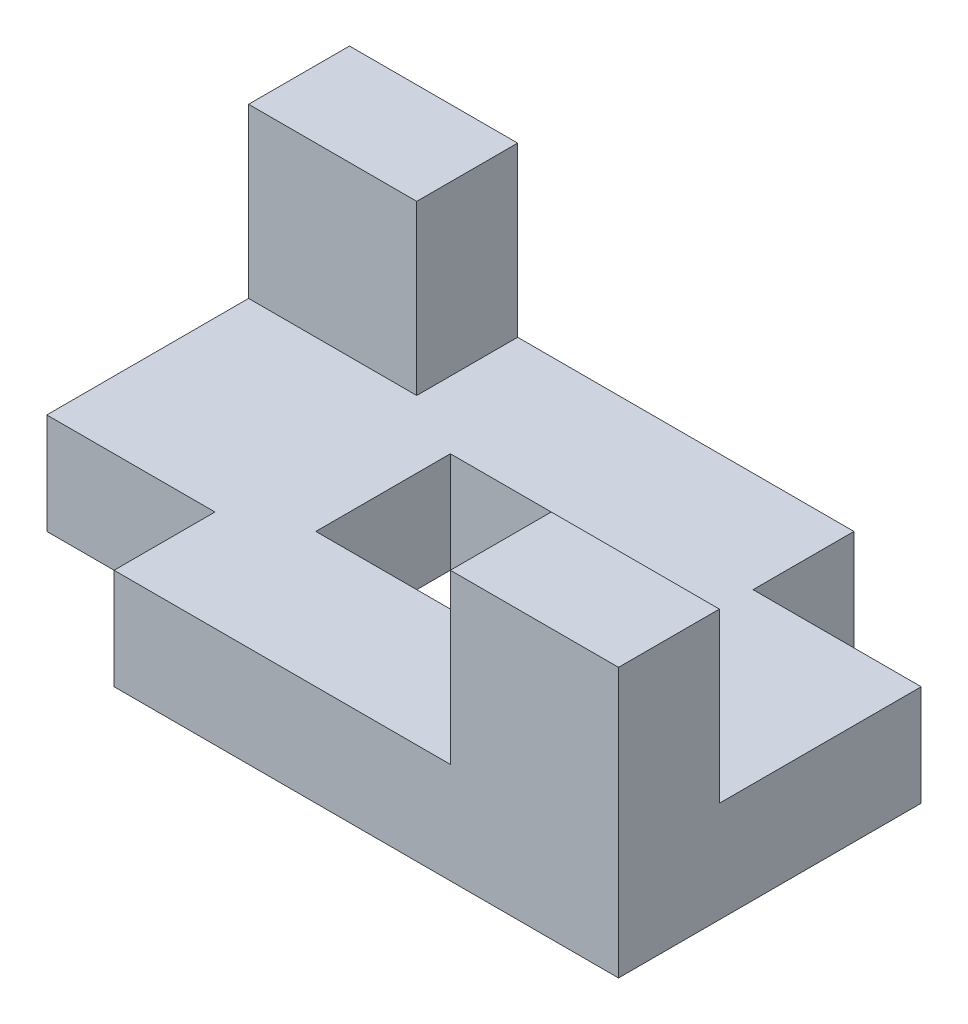
SolidWorks part; units mm, degrees
ref_plane "Front Plane" through (0, 0, 0) normal (0, 0, 1) x (1, 0, 0)
ref_plane "Top Plane" through (0, 0, 0) normal (0, 1, 0) x (1, 0, 0)
ref_plane "Right Plane" through (0, 0, 0) normal (1, 0, 0) x (0, 0, -1)
sketch "Sketch1" plane through (0, 0, 0) normal (0, 1, 0) x (1, 0, 0)
  line L1 (-50, 30) -> (50, 30)
  line L2 (-50, 30) -> (-50, -30)
  line L3 (-50, -30) -> (50, -30)
  line L4 (50, 30) -> (50, -30)
  line L5 (-50, 30) -> (50, -30) construction
  line L6 (-50, -30) -> (50, 30) construction
  point P0 (0, 0)
  dimension "D1" = 100
  dimension "D2" = 60
extrude "Boss-Extrude1" add sketch "Sketch1" along normal blind 15
sketch "Sketch2" plane through (0, 15, 0) normal (0, 1, 0) x (1, 0, 0)
  line L1 (-50, 30) -> (-25, 30)
  line L2 (-50, 30) -> (-50, 15)
  line L3 (-50, 15) -> (-25, 15)
  line L4 (-25, 30) -> (-25, 15)
  line L5 (-50, 30) -> (-25, 15) construction
  line L6 (-50, 15) -> (-25, 30) construction
  line L7 (50, -30) -> (25, -30)
  line L8 (50, -30) -> (50, -15)
  line L9 (50, -15) -> (25, -15)
  line L10 (25, -30) -> (25, -15)
  line L11 (50, -30) -> (25, -15) construction
  line L12 (50, -15) -> (25, -30) construction
  point P4 (-37.5, 22.5)
  point P10 (37.5, -22.5)
  dimension "D1" = 25
  dimension "D2" = 15
  dimension "D3" = 15
  dimension "D4" = 25
extrude "Boss-Extrude2" add sketch "Sketch2" along normal blind 25 contours L3 L4 L1 L2
sketch "Sketch4" plane through (0, 15, 0) normal (0, 1, 0) x (1, 0, 0)
  line L1 (50, -30) -> (25, -30)
  line L2 (50, -30) -> (50, -15)
  line L3 (50, -15) -> (25, -15)
  line L4 (25, -30) -> (25, -15)
  line L5 (50, -30) -> (25, -15) construction
  line L6 (50, -15) -> (25, -30) construction
  point P4 (37.5, -22.5)
  dimension "D1" = 25
  dimension "D2" = 15
extrude "Boss-Extrude3" add sketch "Sketch4" along normal blind 25
sketch "Sketch5" plane through (0, 15, 0) normal (0, 1, 0) x (1, 0, 0)
  line L1 (-50, -30) -> (-25, -30)
  line L2 (-50, -30) -> (-50, -15)
  line L3 (-50, -15) -> (-25, -15)
  line L4 (-25, -30) -> (-25, -15)
  line L5 (-50, -30) -> (-25, -15) construction
  line L6 (-50, -15) -> (-25, -30) construction
  point P4 (-37.5, -22.5)
  dimension "D1" = 25
  dimension "D2" = 15
extrude "Cut-Extrude1" cut sketch "Sketch5" against normal blind 25
sketch "Sketch6" plane through (0, 15, 0) normal (0, 1, 0) x (1, 0, 0)
  line L1 (50, 30) -> (25, 30)
  line L2 (50, 30) -> (50, 15)
  line L3 (50, 15) -> (25, 15)
  line L4 (25, 30) -> (25, 15)
  line L5 (50, 30) -> (25, 15) construction
  line L6 (50, 15) -> (25, 30) construction
  point P4 (37.5, 22.5)
  dimension "D1" = 25
  dimension "D2" = 15
extrude "Cut-Extrude2" cut sketch "Sketch6" against normal blind 25
sketch "Sketch7" plane through (0, 15, 0) normal (0, 1, 0) x (1, 0, 0)
  line L0 (-25, -30) -> (25, -30) construction
  line L1 (-15, 10) -> (15, 10)
  line L2 (-15, 10) -> (-15, -10)
  line L3 (-15, -10) -> (15, -10)
  line L4 (15, 10) -> (15, -10)
  line L5 (-15, 10) -> (15, -10) construction
  line L6 (-15, -10) -> (15, 10) construction
  line L7 (-50, 15) -> (-50, -15) construction
  point P0 (0, 0)
  dimension "D1" = 30
  dimension "D2" = 20
  dimension "D3" = 20
  dimension "D4" = 35
extrude "Cut-Extrude3" cut sketch "Sketch7" against normal blind 25
